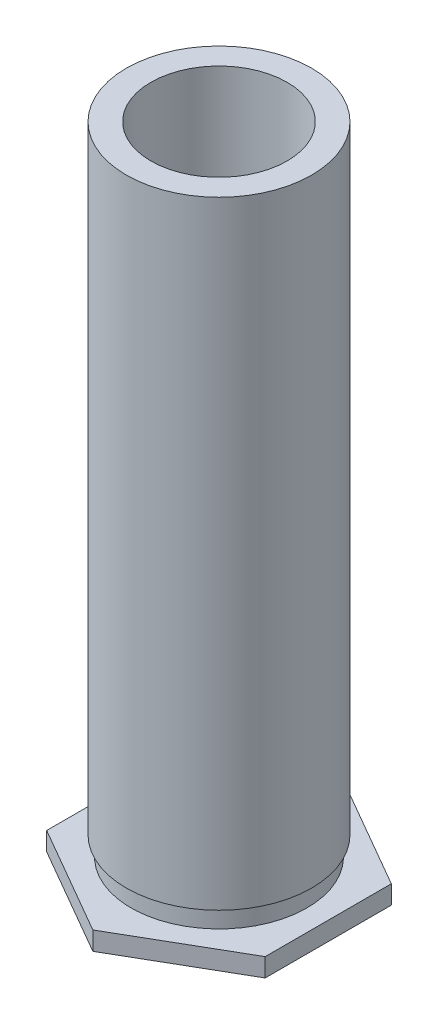
SolidWorks part; units mm, degrees
ref_plane "Plane1" through (0, 0, 0) normal (0, 0, 1) x (1, 0, 0)
ref_plane "Plane2" through (0, 0, 0) normal (0, 1, 0) x (1, 0, 0)
ref_plane "Plane3" through (0, 0, 0) normal (1, 0, 0) x (0, 0, -1)
sketch "BodySke" plane through (0, 0, 0) normal (0, 0, 1) x (1, 0, 0)
  line L0 (2.6924, 0) -> (3.683, 0)
  line L1 (3.683, 0) -> (3.683, 0.5385)
  line L2 (3.683, 0.5385) -> (2.5578, 0.5385)
  line L3 (1.3525, 19.05) -> (1.3526, 0.0051)
  line L4 (2.6924, 1.1039) -> (2.5578, 1.1039)
  line L5 (2.5578, 1.1039) -> (2.5578, 0.5385)
  line L6 (2.6924, 0.0025) -> (2.6924, 0)
  line L7 (1.016, 18.2575) -> (3.6522, 18.2575) construction
  line L8 (2.6924, 19.05) -> (1.3525, 19.05)
  line L9 (0, 0) -> (0, 15.24) construction
  line L10 (2.6924, 0.0025) -> (0, 0.0025)
  line L11 (2.6924, 19.05) -> (2.6924, 1.1039)
  line L12 (0, 0.0051) -> (1.3526, 0.0051)
  line L13 (0, 0.0051) -> (0, 0.0025)
  line L14 (1.016, 0.0051) -> (3.6522, 0.0051) construction
  line L15 (1.016, 0) -> (3.6522, 0) construction
  dimension "D1" = 0.0025
  dimension "E_dia" = 7.366
  dimension "C_dia" = 5.3848
  dimension "Thread_min" = 2.7051
  dimension "Clinching_ht" = 0.5385
  dimension "Advance" = 0.7925
  dimension "Length" = 19.05
  dimension "Thread_limit" = 19.0449
  dimension "Thread_depth" = 19.0449
  dimension "Drill_depth" = 19.05
  dimension "Groove_wid" = 0.5654
  dimension "Groove_dia" = 5.1156
revolve "Body" add sketch "BodySke"
cosmetic thread "ThreadCosmetic" [suppressed]
revolve "EndChamfer" cut sketch "EndChamferSke" angle 360 about L0
sketch "EndChamferSke" plane through (0, 0, 0) normal (0, 0, 1) x (1, 0, 0)
  line L0 (0, -2.54) -> (0, 7.62) construction
  line L1 (0, 0) -> (0, 15.24) construction
  line L2 (1.9812, 11.1252) -> (1.9812, 19.304)
  line L4 (1.9812, 11.1252) -> (1.7526, 11.1252)
  line L6 (1.7526, 11.1252) -> (1.3525, 10.8452)
  line L8 (1.3525, 10.8452) -> (1.3525, 19.304)
  line L9 (1.9812, 19.304) -> (1.3525, 19.304)
  line L10 (2.6924, 19.05) -> (-2.6924, 19.05) construction
  dimension "D1" = 0.254
  dimension "Thread_nominal" = 3.5052
  dimension "D2" = 34.99
  dimension "Thread_min" = 2.7051
  dimension "Inset" = 7.9248
  dimension "B_dia" = 3.9624
revolve "TapDrill" cut sketch "TapDriSke" angle 360 about L0
sketch "TapDriSke" plane through (0, 0, 0) normal (0, 0, 1) x (1, 0, 0)
  line L0 (0, 0) -> (0, 15.24) construction
  line L1 (0, 0) -> (0, 15.24) construction
  line L2 (1.3526, -3.9573) -> (1.3526, 19.05)
  line L3 (2.6924, 19.05) -> (-2.6924, 19.05) construction
  line L4 (1.3526, -3.9573) -> (0, -4.5176)
  line L5 (0, -4.5176) -> (0, 19.05)
  line L6 (0, 19.05) -> (1.3526, 19.05)
  line L7 (1.3526, 0.0051) -> (1.3526, 19.05) construction
  line L8 (0, -4.5176) -> (-1.3526, -3.9573) construction
  line L9 (-1.3526, 19.05) -> (-1.3526, 0.0051) construction
  dimension "D1" = 135
  dimension "Depth" = 23.0073
ref_plane "Plane4" through (0, -0.5486, 0) normal (0, 1, 0) x (-1, 0, 0)
sketch "ThdSchSke" plane through (0, 0, 0) normal (0, 0, 1) x (1, 0, 0)
  line L0 (0, -5.08) -> (0, 7.62) construction
  line L1 (0, 0) -> (0, 15.24) construction
  line L2 (0, 11.1252) -> (1.7526, 11.1252) construction
  line L4 (1.7526, 11.1252) -> (1.3525, 11.4053)
  line L5 (1.9812, 11.1252) -> (-1.9812, 11.1252) construction
  line L6 (1.7526, 11.1252) -> (1.3525, 10.8451)
  line L7 (1.3525, 11.4053) -> (1.3525, 10.8451)
  dimension "Vee_angle" = 70
  dimension "Thread_nominal" = 3.5052
  dimension "Thread_min" = 2.7051
revolve "ThreadSchematic" [suppressed] cut sketch "ThdSchSke" angle 360 about L0
pattern_linear "ThdSchPat" [suppressed]
sketch "HexDieSke" plane through (0, 0.5385, 0) normal (0, 1, 0) x (-1, 0, 0)
  line L0 (0, 3.6662) -> (3.175, 1.8331)
  line L1 (3.175, 1.8331) -> (3.175, -1.8331)
  line L2 (3.175, -1.8331) -> (0, -3.6662)
  line L3 (0, -3.6662) -> (-3.175, -1.8331)
  line L4 (-3.175, -1.8331) -> (-3.175, 1.8331)
  line L5 (-3.175, 1.8331) -> (0, 3.6662)
  circle A1 centre (0, 0) radius 3.175 construction
  circle A2 centre (0, 0) radius 3.6662 construction
  circle A3 centre (0, 0) radius 3.6957
  dimension "Width_across_flats" = 6.35
  dimension "OD" = 7.3914
extrude "HexDie" cut sketch "HexDieSke" against normal blind 0.5385
equation "' \"Length@BodySke\" = 0.75"
equation "' \"B_dia@EndChamferSke\" = 0.203"
equation "' \"C_dia@BodySke\" = 0.28"
equation "' \"Width_across_flats@HexDieSke\" = 0.312"
equation "' \"Inset@EndChamferSke\" = 0.312"
equation "' \"Advance@BodySke\" = 0.0312"
equation "' \"Thread_min@BodySke\" = 0.1528"
equation "' \"Thread_nominal@ThreadCosmetic\" = 0.19"
equation "\"E_dia@BodySke\" = \"Width_across_flats@HexDieSke\" * 1.16"
equation "\"Drill_depth@BodySke\" = \"Length@BodySke\""
equation "\"Thread_depth@BodySke\" = \"Length@BodySke\" - 0.0002"
equation "\"Clinching_ht@BodySke\" = \"C_dia@BodySke\" * 0.1"
equation "\"Groove_dia@BodySke\" = \"C_dia@BodySke\" * 0.95"
equation "\"Groove_wid@BodySke\" = \"Clinching_ht@BodySke\" * 1.05"
equation "\"Thread_limit@BodySke\" = ((sgn( \"Length@BodySke\" - \"Thread_depth@BodySke\" )-1)*( \"Length@BodySke\" - \"Thread_depth@BodySke\" ))/-2+ \"Thread_depth@BodySke\""
equation "\"Depth@TapDriSke\" = \"Thread_limit@BodySke\" + \"Advance@BodySke\" * 5"
equation "\"Depth@TapDriSke\" = ((sgn( \"Depth@TapDriSke\" - \"Drill_depth@BodySke\" )+1)*( \"Depth@TapDriSke\" - \"Drill_depth@BodySke\" ))/2 +\"Drill_depth@BodySke\""
equation "\"Depth@HexDie\" = \"Clinching_ht@BodySke\""
equation "\"OD@HexDieSke\" =  \"Width_across_flats@HexDieSke\" * 1.16 + 0.001"
equation "\"Thread_nominal@EndChamferSke\" = \"Thread_nominal@ThreadCosmetic\""
equation "\"Thread_min@EndChamferSke\" = \"Thread_min@BodySke\""
equation "\"D2@EndChamferSke\" = \"Vee_angle@ThdSchSke\" / 2 - 0.01"
equation "\"Thread_nominal@ThdSchSke\" = \"Thread_nominal@ThreadCosmetic\""
equation "\"Thread_min@ThdSchSke\" = \"Thread_min@BodySke\""
equation "\"Num_threads@ThdSchPat\" = int(  ( \"Thread_limit@BodySke\" - \"Inset@EndChamferSke\" ) / \"Advance@BodySke\" + 0.999 )  + 1"
equation "\"Advance@ThdSchPat\" = (  \"Thread_limit@BodySke\" - \"Inset@EndChamferSke\" ) /  (\"Num_threads@ThdSchPat\" - 1) 'relax it"
